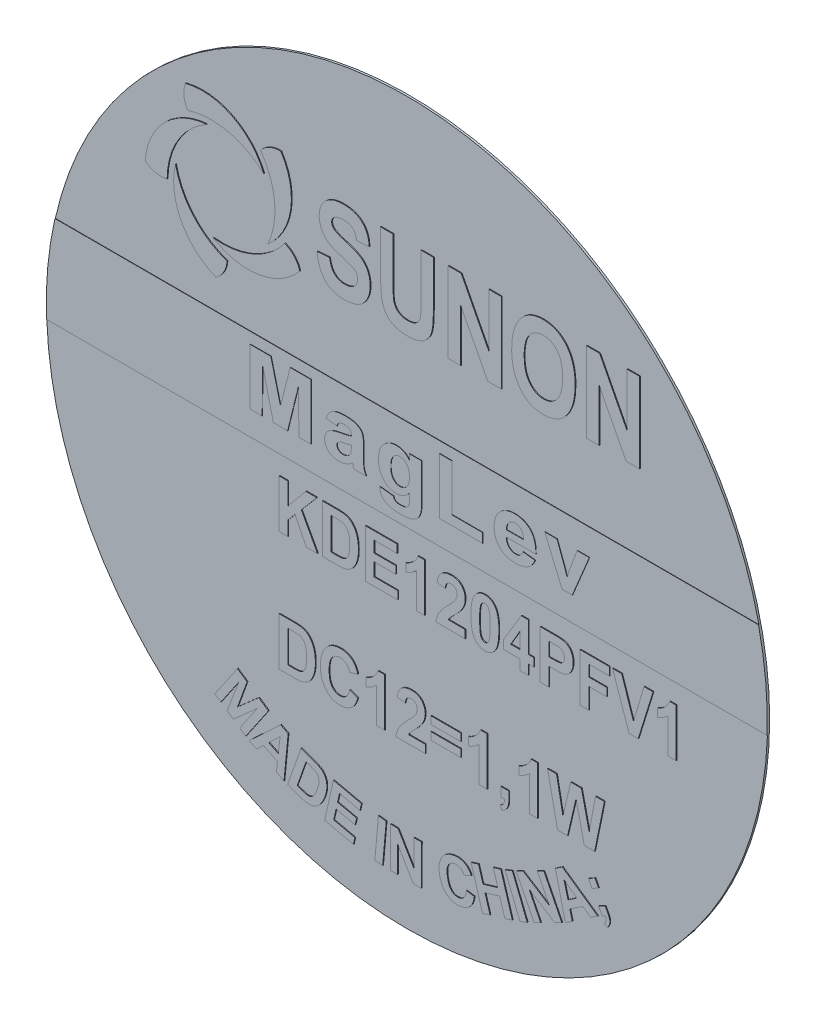
SolidWorks part; units mm, degrees
material "PET"
ref_plane "Front" through (0, 0, 0) normal (0, 0, 1) x (1, 0, 0)
ref_plane "Top" through (0, 0, 0) normal (0, 1, 0) x (1, 0, 0)
ref_plane "Right" through (0, 0, 0) normal (1, 0, 0) x (0, 0, -1)
sketch "Эскиз1" plane through (0, 0, 0) normal (0, 0, 1) x (1, 0, 0)
  circle A0 centre (0, 0) radius 9
  dimension "D1" = 18
extrude "Бобышка-Вытянуть1" add sketch "Эскиз1" along normal blind 0.05
sketch "Эскиз2" plane through (0, 0, 0.05) normal (0, 0, 1) x (1, 0, 0)
  arc A0 (-4.8588, -6.2452) -> (4.8833, -6.2452) centre (0.0123, -0.0965) ccw construction
  arc A2 (-5.5151, 6.5319) -> (-3.5562, 5.5539) centre (-5.0958, 4.9209) cw
  arc A4 (-5.4535, 5.9772) -> (-3.5562, 5.5539) centre (-4.8709, 4.1247) cw
  arc A5 (-5.5151, 6.5319) -> (-5.4535, 5.9772) centre (-4.9377, 6.3153) ccw
  circle A6 centre (-4.5148, 4.7517) radius 1.25 construction
  arc A7 (-3.1308, 6.2532) -> (-3.4556, 4.0879) centre (-4.5334, 5.3566) cw
  arc A8 (-3.1308, 6.2532) -> (-3.6393, 6.0232) centre (-3.1584, 5.6371) ccw
  arc A9 (-3.6393, 6.0232) -> (-3.4556, 4.0879) centre (-5.2212, 4.8967) cw
  arc A10 (-2.6591, 3.8995) -> (-4.8188, 3.5392) centre (-3.9453, 4.9563) cw
  arc A12 (-2.6591, 3.8995) -> (-3.035, 4.312) centre (-3.2536, 3.7353) ccw
  arc A15 (-3.035, 4.312) -> (-4.8188, 3.5392) centre (-4.5952, 5.4683) cw
  arc A16 (-4.7519, 2.7235) -> (-5.7619, 4.6662) centre (-4.1442, 4.2733) cw
  arc A17 (-4.7519, 2.7235) -> (-4.4757, 3.2084) centre (-5.0917, 3.2381) ccw
  arc A18 (-4.4757, 3.2084) -> (-5.7619, 4.6662) centre (-3.8581, 5.0496) cw
  arc A19 (-6.517, 4.3504) -> (-4.9815, 5.9113) centre (-4.8553, 4.2514) cw
  arc A20 (-6.517, 4.3504) -> (-5.9704, 4.2376) centre (-6.1326, 4.8327) ccw
  arc A21 (-5.9704, 4.2376) -> (-4.9815, 5.9113) centre (-4.0285, 4.2192) cw
  text T0 "SUNON" font "Arial Narrow" height 2
  text T1 "KDE1204PFV1\r\nDC12=1,1W" font "Arial Narrow" height 1.2
  text T2 "MADE IN CHINA;)" font "Arial Narrow" height 1
  text T3 "MagLev" font "Arial" height 1.4
  point P40 (-4.5148, 4.7517)
  dimension "D1" = 2.5
  dimension "D2" = 5
extrude "Бобышка-Вытянуть2" add sketch "Эскиз2" along normal blind 0.02
sketch "Эскиз3" plane through (0, 0, 0.05) normal (0, 0, 1) x (1, 0, 0)
  line L0 (-8.7818, 1.9697) -> (8.7818, 1.9697)
  line L1 (-10.1071, 1.9697) -> (9.8757, 1.9697) construction
  line L2 (-10.1071, 1.9697) -> (-10.1071, -0.3149) construction
  line L3 (-10.1071, -0.3149) -> (9.8757, -0.3149) construction
  line L4 (9.8757, 1.9697) -> (9.8757, -0.3149) construction
  line L5 (-0.1157, -0.3149) -> (-0.1157, 1.9697) construction
  line L6 (-10.1071, 0.8274) -> (9.8757, 0.8274) construction
  line L7 (-8.9945, -0.3149) -> (8.9945, -0.3149)
  circle A0 centre (0, 0) radius 9 construction
  arc A1 (-8.7818, 1.9697) -> (-8.9945, -0.3149) centre (0, 0) ccw
  arc A2 (8.7818, 1.9697) -> (8.9945, -0.3149) centre (0, 0) cw
  point P0 (-0.1157, 0.8274)
  dimension "D1" = 2.2846
  dimension "D2" = 19.9828
extrude "Бобышка-Вытянуть3" add sketch "Эскиз3" along normal blind 0.01
